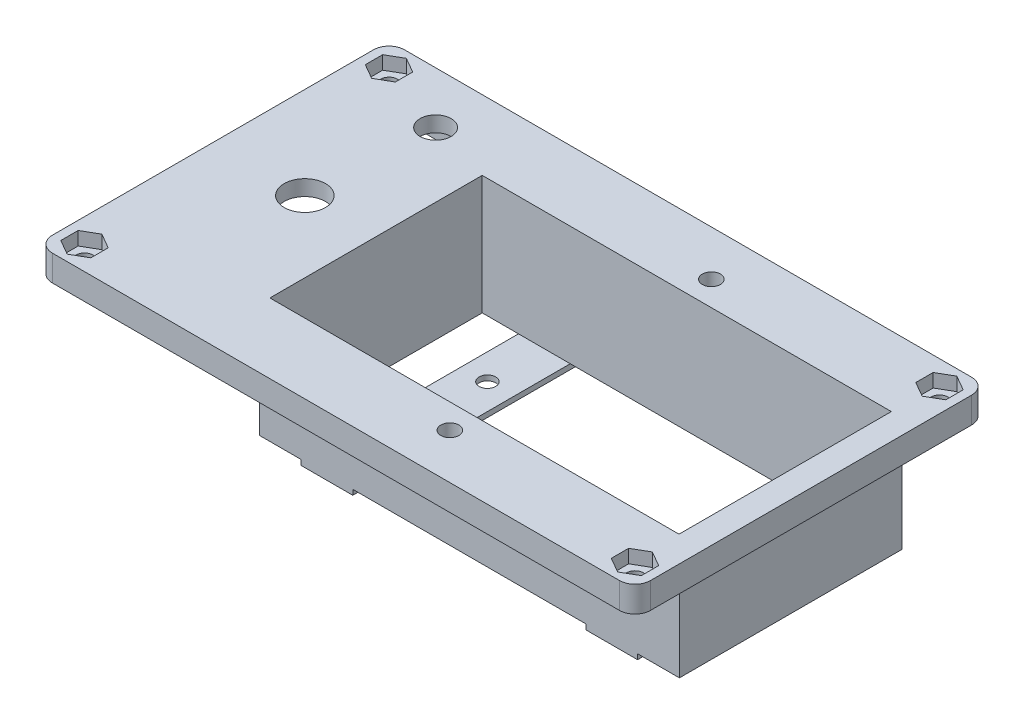
SolidWorks part; units mm, degrees
ref_plane "Спереди" through (0, 0, 0) normal (0, 0, 1) x (1, 0, 0)
ref_plane "Сверху" through (0, 0, 0) normal (0, 1, 0) x (1, 0, 0)
ref_plane "Справа" through (0, 0, 0) normal (1, 0, 0) x (0, 0, -1)
sketch "Эскиз1" plane through (0, 0, 0) normal (0, 1, 0) x (1, 0, 0)
  line L0 (55.0778, 28.0031) -> (55.0778, -25.9969)
  line L1 (55.0778, -25.9969) -> (52.5778, -25.9969)
  line L2 (51.0778, -27.4969) -> (51.0778, -29.9969)
  line L3 (55.0778, -32.9969) -> (-54.4222, -32.9969)
  line L4 (51.0778, -29.9969) -> (-50.4222, -29.9969)
  line L5 (-50.4222, -29.9969) -> (-50.4222, -27.4969)
  line L6 (-51.9222, -25.9969) -> (-54.4222, -25.9969)
  line L7 (-54.4222, -25.9969) -> (-54.4222, 28.0031)
  line L8 (-54.4222, 28.0031) -> (-51.9222, 28.0031)
  line L9 (-50.4222, 29.5031) -> (-50.4222, 32.0031)
  line L10 (-50.4222, 32.0031) -> (51.0778, 32.0031)
  line L11 (51.0778, 32.0031) -> (51.0778, 29.5031)
  line L12 (52.5778, 28.0031) -> (55.0778, 28.0031)
  line L13 (58.0778, 32.0031) -> (58.0778, -29.9969)
  line L14 (-54.4222, 35.0031) -> (55.0778, 35.0031)
  line L15 (-57.4222, -29.9969) -> (-57.4222, 32.0031)
  arc A0 (52.5778, -25.9969) -> (51.0778, -27.4969) centre (52.5778, -27.4969) ccw
  circle A1 centre (53.4778, -28.3969) radius 1.6
  arc A2 (55.0778, -32.9969) -> (58.0778, -29.9969) centre (55.0778, -29.9969) ccw
  arc A3 (-50.4222, -27.4969) -> (-51.9222, -25.9969) centre (-51.9222, -27.4969) ccw
  circle A4 centre (-52.8222, -28.3969) radius 1.6
  arc A5 (-57.4222, -29.9969) -> (-54.4222, -32.9969) centre (-54.4222, -29.9969) ccw
  arc A6 (-51.9222, 28.0031) -> (-50.4222, 29.5031) centre (-51.9222, 29.5031) ccw
  circle A7 centre (-52.8222, 30.4031) radius 1.6
  arc A8 (51.0778, 29.5031) -> (52.5778, 28.0031) centre (52.5778, 29.5031) ccw
  circle A9 centre (53.4778, 30.4031) radius 1.6
  arc A10 (58.0778, 32.0031) -> (55.0778, 35.0031) centre (55.0778, 32.0031) ccw
  arc A11 (-54.4222, 35.0031) -> (-57.4222, 32.0031) centre (-54.4222, 32.0031) ccw
  point P40 (-57.4222, 1.0031)
  point P41 (0.3278, 35.0031)
  point P42 (0, 0)
  dimension "D3" = 3.2
  dimension "D1" = 115.5
  dimension "D2" = 68
extrude "Бобышка-Вытянуть1" add sketch "Эскиз1" along normal blind 2
sketch "Эскиз2" plane through (0, 2, 0) normal (0, 1, 0) x (1, 0, 0)
  line L0 (-54.4222, -25.9969) -> (-51.9222, -25.9969) construction
  line L1 (-54.4222, 28.0031) -> (-54.4222, -25.9969) construction
  line L2 (-51.9222, 28.0031) -> (-54.4222, 28.0031) construction
  line L3 (-50.4222, 32.0031) -> (-50.4222, 29.5031) construction
  line L4 (51.0778, 32.0031) -> (-50.4222, 32.0031) construction
  line L5 (51.0778, 29.5031) -> (51.0778, 32.0031) construction
  line L6 (55.0778, 28.0031) -> (52.5778, 28.0031) construction
  line L7 (55.0778, -25.9969) -> (55.0778, 28.0031) construction
  line L8 (52.5778, -25.9969) -> (55.0778, -25.9969) construction
  line L9 (51.0778, -29.9969) -> (51.0778, -27.4969) construction
  line L10 (-50.4222, -29.9969) -> (51.0778, -29.9969) construction
  line L11 (-50.4222, -27.4969) -> (-50.4222, -29.9969) construction
  line L12 (51.0778, 29.5031) -> (51.0778, 32.0031)
  line L13 (55.0778, 28.0031) -> (52.5778, 28.0031)
  line L14 (55.0778, -25.9969) -> (55.0778, 28.0031)
  line L15 (52.5778, -25.9969) -> (55.0778, -25.9969)
  line L16 (51.0778, -29.9969) -> (51.0778, -27.4969)
  line L17 (-50.4222, -29.9969) -> (51.0778, -29.9969)
  line L18 (-50.4222, -27.4969) -> (-50.4222, -29.9969)
  line L19 (-54.4222, -25.9969) -> (-51.9222, -25.9969)
  line L20 (51.0778, 32.0031) -> (-50.4222, 32.0031)
  line L21 (-50.4222, 32.0031) -> (-50.4222, 29.5031)
  line L22 (-51.9222, 28.0031) -> (-54.4222, 28.0031)
  line L23 (-54.4222, 28.0031) -> (-54.4222, -25.9969)
  arc A0 (-51.9222, 28.0031) -> (-50.4222, 29.5031) centre (-51.9222, 29.5031) ccw construction
  arc A1 (51.0778, 29.5031) -> (52.5778, 28.0031) centre (52.5778, 29.5031) ccw construction
  arc A2 (52.5778, -25.9969) -> (51.0778, -27.4969) centre (52.5778, -27.4969) ccw construction
  arc A3 (-50.4222, -27.4969) -> (-51.9222, -25.9969) centre (-51.9222, -27.4969) ccw construction
  arc A4 (51.0778, 29.5031) -> (52.5778, 28.0031) centre (52.5778, 29.5031) ccw
  arc A5 (52.5778, -25.9969) -> (51.0778, -27.4969) centre (52.5778, -27.4969) ccw
  arc A6 (-50.4222, -27.4969) -> (-51.9222, -25.9969) centre (-51.9222, -27.4969) ccw
  arc A7 (-51.9222, 28.0031) -> (-50.4222, 29.5031) centre (-51.9222, 29.5031) ccw
extrude "Вытянуть-Тонкостенный1" add sketch "Эскиз2" against normal blind 4 thin thin type one direction reverse wall 2
sketch "Эскиз3" plane through (0, -2, 0) normal (0, -1, 0) x (1, 0, 0)
  line L0 (51.0778, 29.9969) -> (51.0778, 27.4969) construction
  line L1 (52.5778, 25.9969) -> (55.0778, 25.9969) construction
  line L2 (55.0778, 25.9969) -> (55.0778, -28.0031) construction
  line L3 (55.0778, -28.0031) -> (52.5778, -28.0031) construction
  line L4 (51.0778, -29.5031) -> (51.0778, -32.0031) construction
  line L5 (51.0778, -32.0031) -> (-50.4222, -32.0031) construction
  line L6 (-50.4222, -32.0031) -> (-50.4222, -29.5031) construction
  line L7 (-51.9222, -28.0031) -> (-54.4222, -28.0031) construction
  line L8 (-54.4222, -28.0031) -> (-54.4222, 25.9969) construction
  line L9 (-50.4222, 29.9969) -> (51.0778, 29.9969) construction
  line L10 (-50.4222, 27.4969) -> (-50.4222, 29.9969) construction
  line L11 (-54.4222, 25.9969) -> (-51.9222, 25.9969) construction
  line L12 (51.0778, 29.9969) -> (51.0778, 27.4969)
  line L13 (52.5778, 25.9969) -> (55.0778, 25.9969)
  line L14 (55.0778, 25.9969) -> (55.0778, -28.0031)
  line L15 (55.0778, -28.0031) -> (52.5778, -28.0031)
  line L16 (51.0778, -29.5031) -> (51.0778, -32.0031)
  line L17 (51.0778, -32.0031) -> (-50.4222, -32.0031)
  line L18 (-50.4222, -32.0031) -> (-50.4222, -29.5031)
  line L19 (-51.9222, -28.0031) -> (-54.4222, -28.0031)
  line L20 (-54.4222, -28.0031) -> (-54.4222, 25.9969)
  line L21 (-50.4222, 29.9969) -> (51.0778, 29.9969)
  line L22 (-50.4222, 27.4969) -> (-50.4222, 29.9969)
  line L23 (-54.4222, 25.9969) -> (-51.9222, 25.9969)
  arc A0 (51.0778, 27.4969) -> (52.5778, 25.9969) centre (52.5778, 27.4969) ccw construction
  arc A1 (52.5778, -28.0031) -> (51.0778, -29.5031) centre (52.5778, -29.5031) ccw construction
  arc A2 (-50.4222, -29.5031) -> (-51.9222, -28.0031) centre (-51.9222, -29.5031) ccw construction
  arc A3 (-51.9222, 25.9969) -> (-50.4222, 27.4969) centre (-51.9222, 27.4969) ccw construction
  arc A4 (51.0778, 27.4969) -> (52.5778, 25.9969) centre (52.5778, 27.4969) ccw
  arc A5 (52.5778, -28.0031) -> (51.0778, -29.5031) centre (52.5778, -29.5031) ccw
  arc A6 (-50.4222, -29.5031) -> (-51.9222, -28.0031) centre (-51.9222, -29.5031) ccw
  arc A7 (-51.9222, 25.9969) -> (-50.4222, 27.4969) centre (-51.9222, 27.4969) ccw
extrude "Вырез-Вытянуть-Тонкостенный5" cut sketch "Эскиз3" against normal blind 2.01 thin thin type one direction wall 0.2
sketch "Эскиз4" plane through (0, 2, 0) normal (0, 1, 0) x (1, 0, 0)
  line L0 (-54.4222, -32.9969) -> (55.0778, -32.9969) construction
  line L1 (58.0778, -29.9969) -> (58.0778, 32.0031) construction
  line L2 (-57.4222, 32.0031) -> (-57.4222, -29.9969) construction
  line L3 (55.0778, 35.0031) -> (-54.4222, 35.0031) construction
  line L4 (-54.4222, -32.9969) -> (55.0778, -32.9969)
  line L5 (58.0778, -29.9969) -> (58.0778, 32.0031)
  line L6 (-57.4222, 32.0031) -> (-57.4222, -29.9969)
  line L7 (55.0778, 35.0031) -> (-54.4222, 35.0031)
  arc A0 (-57.4222, -29.9969) -> (-54.4222, -32.9969) centre (-54.4222, -29.9969) ccw construction
  circle A1 centre (-52.8222, -28.3969) radius 1.6 construction
  circle A2 centre (53.4778, -28.3969) radius 1.6 construction
  arc A3 (55.0778, -32.9969) -> (58.0778, -29.9969) centre (55.0778, -29.9969) ccw construction
  arc A4 (58.0778, 32.0031) -> (55.0778, 35.0031) centre (55.0778, 32.0031) ccw construction
  circle A5 centre (53.4778, 30.4031) radius 1.6 construction
  circle A6 centre (-52.8222, 30.4031) radius 1.6 construction
  arc A7 (-54.4222, 35.0031) -> (-57.4222, 32.0031) centre (-54.4222, 32.0031) ccw construction
  arc A8 (-57.4222, -29.9969) -> (-54.4222, -32.9969) centre (-54.4222, -29.9969) ccw
  circle A9 centre (-52.8222, -28.3969) radius 1.6
  circle A10 centre (53.4778, -28.3969) radius 1.6
  arc A11 (55.0778, -32.9969) -> (58.0778, -29.9969) centre (55.0778, -29.9969) ccw
  arc A12 (58.0778, 32.0031) -> (55.0778, 35.0031) centre (55.0778, 32.0031) ccw
  circle A13 centre (53.4778, 30.4031) radius 1.6
  circle A14 centre (-52.8222, 30.4031) radius 1.6
  arc A15 (-54.4222, 35.0031) -> (-57.4222, 32.0031) centre (-54.4222, 32.0031) ccw
extrude "Бобышка-Вытянуть2" add sketch "Эскиз4" along normal blind 3
sketch "Эскиз5" plane through (0, 5, 0) normal (0, 1, 0) x (1, 0, 0)
  line L0 (0.3278, 35.0031) -> (0.3278, -32.9969) construction
  line L1 (-52.8222, 27.0545) -> (-49.9222, 28.7288)
  line L2 (-49.9222, 28.7288) -> (-49.9222, 32.0774)
  line L3 (-49.9222, 32.0774) -> (-52.8222, 33.7517)
  line L4 (-52.8222, 33.7517) -> (-55.7222, 32.0774)
  line L5 (-55.7222, 32.0774) -> (-55.7222, 28.7288)
  line L6 (-55.7222, 28.7288) -> (-52.8222, 27.0545)
  line L7 (55.0778, 35.0031) -> (-54.4222, 35.0031) construction
  line L8 (-54.4222, -32.9969) -> (55.0778, -32.9969) construction
  line L9 (-57.4222, 1.0031) -> (58.0778, 1.0031) construction
  line L10 (-57.4222, 32.0031) -> (-57.4222, -29.9969) construction
  line L11 (58.0778, -29.9969) -> (58.0778, 32.0031) construction
  line L12 (56.3778, 28.7288) -> (53.4778, 27.0545)
  line L13 (56.3778, 32.0774) -> (56.3778, 28.7288)
  line L14 (53.4778, 33.7517) -> (56.3778, 32.0774)
  line L15 (50.5778, 32.0774) -> (53.4778, 33.7517)
  line L16 (50.5778, 28.7288) -> (50.5778, 32.0774)
  line L17 (53.4778, 27.0545) -> (50.5778, 28.7288)
  line L18 (53.4778, -25.0483) -> (50.5778, -26.7226)
  line L19 (50.5778, -26.7226) -> (50.5778, -30.0712)
  line L20 (50.5778, -30.0712) -> (53.4778, -31.7455)
  line L21 (53.4778, -31.7455) -> (56.3778, -30.0712)
  line L22 (56.3778, -30.0712) -> (56.3778, -26.7226)
  line L23 (56.3778, -26.7226) -> (53.4778, -25.0483)
  line L24 (-55.7222, -26.7226) -> (-52.8222, -25.0483)
  line L25 (-55.7222, -30.0712) -> (-55.7222, -26.7226)
  line L26 (-52.8222, -31.7455) -> (-55.7222, -30.0712)
  line L27 (-49.9222, -30.0712) -> (-52.8222, -31.7455)
  line L28 (-49.9222, -26.7226) -> (-49.9222, -30.0712)
  line L29 (-52.8222, -25.0483) -> (-49.9222, -26.7226)
  circle A0 centre (-52.8222, 30.4031) radius 2.9 construction
  circle A1 centre (53.4778, 30.4031) radius 2.9 construction
  circle A2 centre (53.4778, -28.3969) radius 2.9 construction
  circle A3 centre (-52.8222, -28.3969) radius 2.9 construction
extrude "Вырез-Вытянуть1" cut sketch "Эскиз5" against normal blind 2.6
sketch "Эскиз6" plane through (0, 5, 0) normal (0, 1, 0) x (1, 0, 0)
  line L0 (-57.4222, 1.0031) -> (58.0778, 1.0031) construction
  line L1 (-57.4222, 32.0031) -> (-57.4222, -29.9969) construction
  line L2 (58.0778, -29.9969) -> (58.0778, 32.0031) construction
  line L4 (53.0778, 21.5031) -> (-25.9222, 21.5031)
  line L5 (53.0778, 21.5031) -> (53.0778, -19.4969)
  line L6 (53.0778, -19.4969) -> (-25.9222, -19.4969)
  line L7 (-25.9222, 21.5031) -> (-25.9222, -19.4969)
  line L8 (53.0778, 21.5031) -> (-25.9222, -19.4969) construction
  line L9 (53.0778, -19.4969) -> (-25.9222, 21.5031) construction
  point P6 (13.5778, 1.0031)
  point P11 (53.0778, 1.0031)
  dimension "D1" = 79
  dimension "D2" = 41
  dimension "D3" = 5
extrude "Вырез-Вытянуть2" cut sketch "Эскиз6" against normal through all
sketch "Эскиз7" plane through (0, 2, 0) normal (0, -1, 0) x (1, 0, 0)
  line L1 (53.0778, -21.5031) -> (-25.9222, -21.5031)
  line L2 (53.0778, -21.5031) -> (53.0778, 19.4969)
  line L3 (53.0778, 19.4969) -> (-25.9222, 19.4969)
  line L4 (-25.9222, -21.5031) -> (-25.9222, 19.4969)
  line L5 (53.0778, -21.5031) -> (-25.9222, 19.4969) construction
  line L6 (53.0778, 19.4969) -> (-25.9222, -21.5031) construction
  line L7 (-26.9222, 20.4969) -> (54.1543, 20.4969)
  line L8 (-26.9222, 20.4969) -> (-26.9222, -22.5031)
  line L9 (-26.9222, -22.5031) -> (54.1543, -22.5031)
  line L10 (54.1543, 20.4969) -> (54.1543, -22.5031)
  point P0 (13.5778, -1.0031)
  point P10 (13.5778, 19.4969)
  point P11 (13.6161, 20.4969)
  point P12 (13.5778, -21.5031)
  point P13 (-26.9222, -1.0031)
  dimension "D1" = 1
  dimension "D2" = 1
  dimension "D3" = 1
extrude "Бобышка-Вытянуть3" add sketch "Эскиз7" along normal blind 20
sketch "Эскиз9" plane through (0, 2, 0) normal (0, -1, 0) x (1, 0, 0)
  line L2 (55.0778, -35.0031) -> (-54.4222, -35.0031) construction
  line L3 (-57.4222, -32.0031) -> (-57.4222, 29.9969) construction
  circle A0 centre (-38.4222, -25.0031) radius 3
  dimension "D3" = 19
  dimension "D1" = 6
  dimension "D2" = 10
extrude "Вырез-Вытянуть3" cut sketch "Эскиз9" against normal through all
sketch "Эскиз10" plane through (0, 2, 0) normal (0, -1, 0) x (1, 0, 0)
  line L0 (-52.4222, -1.0031) -> (-26.9222, -1.0031) construction
  line L1 (-52.4222, -26.0031) -> (-52.4222, 23.9969) construction
  line L2 (-26.9222, 20.4969) -> (-26.9222, -22.5031) construction
  circle A0 centre (-39.6722, -1.0031) radius 4
  dimension "D1" = 8
extrude "Вырез-Вытянуть4" cut sketch "Эскиз10" against normal through all
sketch "Эскиз11" plane through (0, -18, 0) normal (0, -1, 0) x (1, 0, 0)
  line L0 (-25.9222, -1.0031) -> (53.0778, -1.0031) construction
  line L1 (-25.9222, 19.4969) -> (-25.9222, -21.5031) construction
  line L2 (53.0778, -21.5031) -> (53.0778, 19.4969) construction
  line L3 (13.5778, 19.4969) -> (13.5778, -21.5031) construction
  line L4 (53.0778, 19.4969) -> (-25.9222, 19.4969) construction
  line L5 (-25.9222, -21.5031) -> (53.0778, -21.5031) construction
  line L6 (53.0778, 20.4969) -> (-26.9222, 20.4969) construction
  line L7 (41.0778, 8.4969) -> (-13.9222, 8.4969) construction
  line L8 (41.0778, 8.4969) -> (41.0778, -10.5031) construction
  line L9 (41.0778, -10.5031) -> (-13.9222, -10.5031) construction
  line L10 (-13.9222, 8.4969) -> (-13.9222, -10.5031) construction
  line L11 (41.0778, 8.4969) -> (-13.9222, -10.5031) construction
  line L12 (41.0778, -10.5031) -> (-13.9222, 8.4969) construction
  line L13 (-8.9222, -22.5031) -> (-18.9222, -22.5031)
  line L14 (-8.9222, -22.5031) -> (-8.9222, 20.4969)
  line L15 (-8.9222, 20.4969) -> (-18.9222, 20.4969)
  line L16 (-18.9222, -22.5031) -> (-18.9222, 20.4969)
  line L17 (-8.9222, -22.5031) -> (-18.9222, 20.4969) construction
  line L18 (-8.9222, 20.4969) -> (-18.9222, -22.5031) construction
  line L19 (36.0778, 20.4969) -> (46.0778, -22.5031) construction
  line L20 (36.0778, -22.5031) -> (46.0778, 20.4969) construction
  line L21 (41.0778, 8.4969) -> (41.0778, -10.5031) construction
  line L22 (46.0778, -22.5031) -> (46.0778, 20.4969)
  line L23 (36.0778, 20.4969) -> (46.0778, 20.4969)
  line L24 (36.0778, -22.5031) -> (36.0778, 20.4969)
  line L25 (36.0778, -22.5031) -> (46.0778, -22.5031)
  circle A0 centre (-13.9222, 8.4969) radius 1.6
  circle A1 centre (-13.9222, -10.5031) radius 1.6
  circle A2 centre (41.0778, -10.5031) radius 1.6
  circle A3 centre (41.0778, 8.4969) radius 1.6
  point P12 (13.5778, -1.0031)
  point P17 (-13.9222, -1.0031)
  point P32 (41.0778, -1.0031)
  dimension "D4" = 3.2
  dimension "D5" = 3.2
  dimension "D1" = 55
  dimension "D2" = 19
  dimension "D3" = 10
extrude "Бобышка-Вытянуть4" add sketch "Эскиз11" along normal blind 1
sketch "Эскиз12" plane through (0, 2, 0) normal (0, -1, 0) x (1, 0, 0)
  line L0 (13.5778, -22.5031) -> (13.5778, 20.4969) construction
  line L1 (-8.9222, -22.5031) -> (36.0778, -22.5031) construction
  line L2 (53.0778, 20.4969) -> (-26.9222, 20.4969) construction
  line L3 (13.5778, -22.5031) -> (13.5778, -30.0031) construction
  line L4 (49.0778, -30.0031) -> (-48.4222, -30.0031) construction
  line L5 (36.0778, 20.4969) -> (-8.9222, 20.4969) construction
  line L6 (13.5778, 20.4969) -> (13.5778, 27.9969) construction
  line L7 (-48.4222, 27.9969) -> (49.0778, 27.9969) construction
  line L8 (13.5778, -29.6017) -> (16.4778, -27.9274)
  line L9 (13.5778, 21.0161) -> (16.3758, 22.6315)
  line L10 (16.3758, 22.6315) -> (16.3758, 25.8623)
  line L11 (16.3758, 25.8623) -> (13.5778, 27.4777)
  line L12 (13.5778, 27.4777) -> (10.7799, 25.8623)
  line L13 (10.7799, 25.8623) -> (10.7799, 22.6315)
  line L14 (10.7799, 22.6315) -> (13.5778, 21.0161)
  line L15 (16.4778, -27.9274) -> (16.4778, -24.5788)
  line L16 (16.4778, -24.5788) -> (13.5778, -22.9045)
  line L17 (13.5778, -22.9045) -> (10.6778, -24.5788)
  line L18 (10.6778, -24.5788) -> (10.6778, -27.9274)
  line L19 (10.6778, -27.9274) -> (13.5778, -29.6017)
  line L20 (18.5778, -30.0031) -> (8.5778, -30.0031)
  line L21 (18.5778, -30.0031) -> (18.5778, -22.5031)
  line L22 (18.5778, -22.5031) -> (8.5778, -22.5031)
  line L23 (8.5778, -30.0031) -> (8.5778, -22.5031)
  line L24 (18.5778, -30.0031) -> (8.5778, -22.5031) construction
  line L25 (18.5778, -22.5031) -> (8.5778, -30.0031) construction
  line L26 (18.5778, 27.9969) -> (8.5778, 27.9969)
  line L27 (18.5778, 27.9969) -> (18.5778, 20.4969)
  line L28 (18.5778, 20.4969) -> (8.5778, 20.4969)
  line L29 (8.5778, 27.9969) -> (8.5778, 20.4969)
  line L30 (18.5778, 27.9969) -> (8.5778, 20.4969) construction
  line L31 (18.5778, 20.4969) -> (8.5778, 27.9969) construction
  circle A0 centre (13.5778, 24.2469) radius 2.7979 construction
  circle A1 centre (13.5778, -26.2531) radius 2.9 construction
  dimension "D1" = 10
extrude "Бобышка-Вытянуть5" add sketch "Эскиз12" along normal blind 3
sketch "Эскиз13" plane through (0, 2, 0) normal (0, -1, 0) x (1, 0, 0)
  circle A0 centre (13.5778, 24.2469) radius 1.75
  circle A1 centre (13.5778, -26.2531) radius 1.75
  dimension "D1" = 3.5
  dimension "D2" = 3.5
extrude "Вырез-Вытянуть5" cut sketch "Эскиз13" against normal through all
